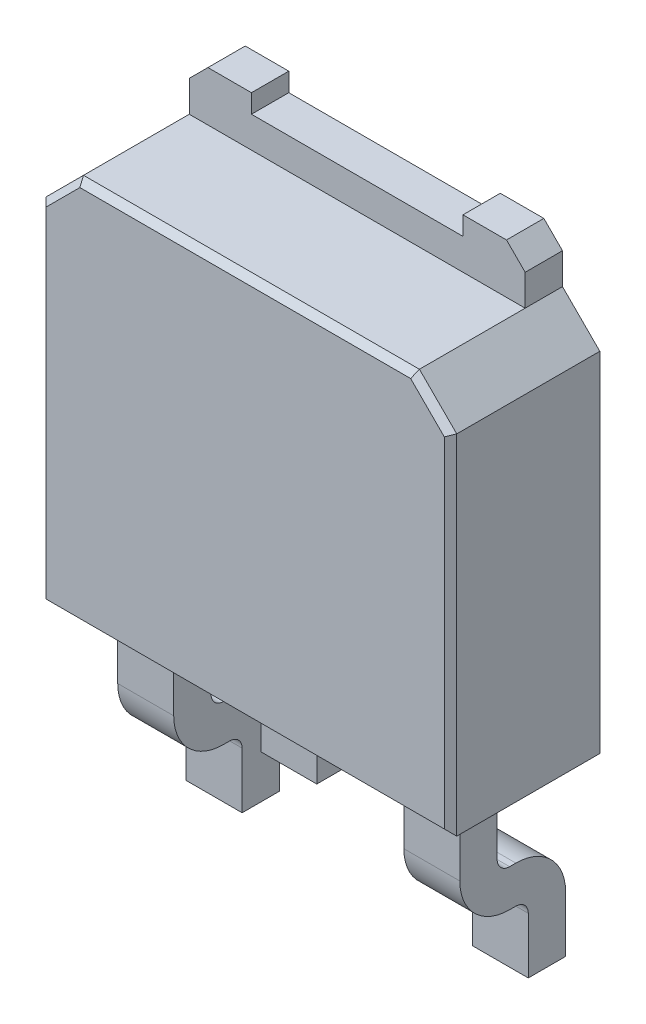
SolidWorks part; units mm, degrees
ref_plane "Vorne" through (0, 0, 0) normal (0, 0, 1) x (1, 0, 0)
ref_plane "Oben" through (0, 0, 0) normal (0, 1, 0) x (1, 0, 0)
ref_plane "Rechts" through (0, 0, 0) normal (1, 0, 0) x (0, 0, -1)
sketch "Skizze1" plane through (0, 0, 0) normal (0, 0, 1) x (1, 0, 0)
  line L1 (-3.3, 3.1) -> (3.3, 3.1)
  line L2 (-3.3, 3.1) -> (-3.3, -3.1)
  line L3 (-3.3, -3.1) -> (3.3, -3.1)
  line L4 (3.3, 3.1) -> (3.3, -3.1)
  point P4 (0, 3.1)
  point P5 (3.3, 0)
  point P6 (3.3, 0)
  dimension "D1" = 6.6
  dimension "D2" = 6.2
extrude "Linear austragen1" add sketch "Skizze1" along normal blind 2.4
chamfer "Fase2" distance 0.6 angle 45 2 edges at (-3.3, 3.1, 1.2) (3.3, 3.1, 1.2)
sketch "Skizze2" plane through (0, -3.1, 0) normal (0, -1, 0) x (1, 0, 0)
  line L1 (1.85, 1.7) -> (2.75, 1.7)
  line L2 (1.85, 1.7) -> (1.85, 1.1)
  line L3 (1.85, 1.1) -> (2.75, 1.1)
  line L4 (2.75, 1.7) -> (2.75, 1.1)
  dimension "D1" = 0.9
  dimension "D2" = 0.6
sketch3d "3D-Skizze1"
  line L0 (2.3, -3.1, 1.4) -> (2.3, -4.3, 1.4)
  line L1 (2.3, -4.8, 0.9) -> (2.3, -4.8, 0.8)
  line L2 (2.3, -5.3, 0.3) -> (2.3, -6.2, 0.3)
  arc A0 (2.3, -4.3, 1.4) -> (2.3, -4.8, 0.9) centre (2.3, -4.3, 0.9) ccw
  arc A1 (2.3, -4.8, 0.8) -> (2.3, -5.3, 0.3) centre (2.3, -5.3, 0.8) ccw
  point P0 (2.3, -3.1, 1.4)
  point P7 (2.3, -4.8, 1.4)
  point P8 (2.8, -4.3, 0.9)
  point P11 (2.3, -4.8, 0.3)
  point P12 (1.8, -5.3, 0.8)
  dimension "D1" = 0.5
  dimension "D2" = 0.5
sweep "Austragung1" add profiles "Skizze2" path "3D-Skizze1"
mirror "Spiegeln1" about plane through (0, 0, 0) normal (1, 0, 0) of "Austragung1"
sketch "Skizze3" plane through (0, -3.1, 0) normal (0, -1, 0) x (1, 0, 0)
  line L1 (-0.45, 1.7) -> (0.45, 1.7)
  line L2 (-0.45, 1.7) -> (-0.45, 1.1)
  line L3 (-0.45, 1.1) -> (0.45, 1.1)
  line L4 (0.45, 1.7) -> (0.45, 1.1)
  dimension "D1" = 0.9
  dimension "D2" = 0.6
extrude "Linear austragen2" add sketch "Skizze3" along normal blind 1
sketch "Skizze4" plane through (0, 3.1, 0) normal (0, 1, 0) x (-1, 0, 0)
  line L0 (-2.7, 0) -> (2.7, 0) construction
  line L1 (-2.7, 0) -> (2.7, 0)
  line L2 (-2.7, 0) -> (-2.7, 0.6)
  line L3 (-2.7, 0.6) -> (2.7, 0.6)
  line L4 (2.7, 0) -> (2.7, 0.6)
  point P6 (0, 0.6)
  dimension "D1" = 5.4
  dimension "D2" = 0.6
extrude "Linear austragen3" add sketch "Skizze4" along normal blind 0.8
sketch "Skizze5" plane through (0, 3.9, 0) normal (0, 1, 0) x (-1, 0, 0)
  line L0 (-2.7, 0) -> (2.7, 0) construction
  line L1 (1.7, 0) -> (-1.7, 0)
  line L2 (1.7, 0) -> (1.7, 0.6)
  line L3 (1.7, 0.6) -> (-1.7, 0.6)
  line L4 (-1.7, 0) -> (-1.7, 0.6)
  line L5 (2.7, 0.6) -> (-2.7, 0.6) construction
  point P8 (0, 0.6)
  dimension "D1" = 3.4
extrude "Schnitt-Linear austragen1" cut sketch "Skizze5" against normal blind 0.3
chamfer "Fase3" distance 0.3 angle 45 2 edges at (-2.7, 3.9, 0.3) (2.7, 3.9, 0.3)
chamfer "Fase4" distance 0.1 angle 45 6 edges at (0, -3.1, 2.4) (-3.3, -0.3, 2.4) (-3, 2.8, 2.4) (0, 3.1, 2.4) (3, 2.8, 2.4) (3.3, -0.3, 2.4)
